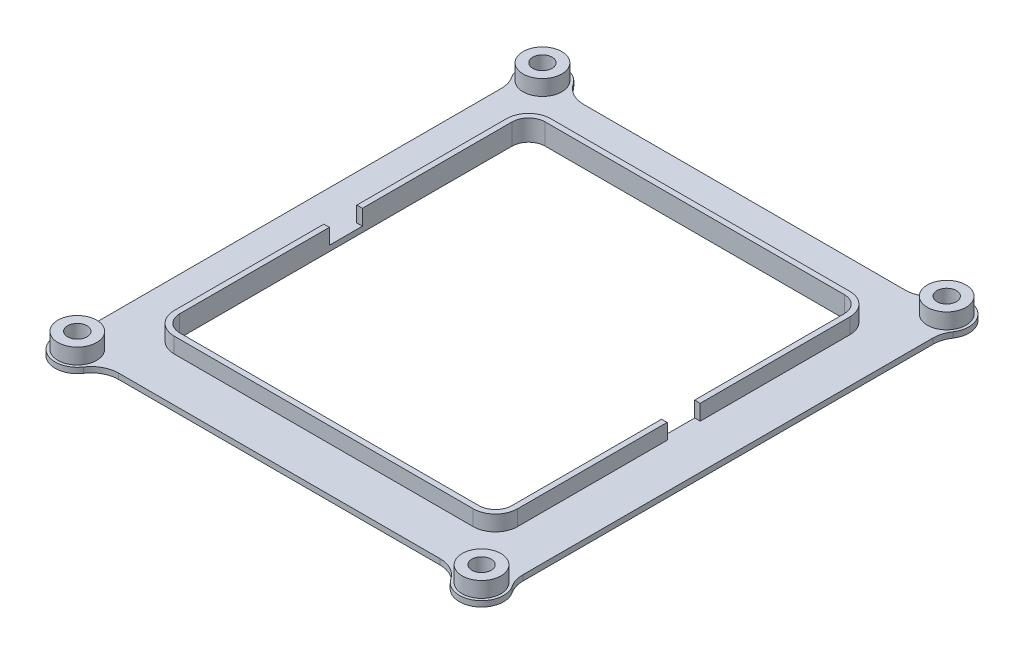
SolidWorks part; units mm, degrees
material "6061-T6 (SS)"
ref_plane "Front Plane" through (0, 0, 0) normal (0, 0, 1) x (1, 0, 0)
ref_plane "Top Plane" through (0, 0, 0) normal (0, 1, 0) x (1, 0, 0)
ref_plane "Right Plane" through (0, 0, 0) normal (1, 0, 0) x (0, 0, -1)
sketch "Sketch1" plane through (0, 0, 0) normal (0, 1, 0) x (1, 0, 0)
  line L0 (-33, 42) -> (33, 42)
  line L1 (-36.5, -42) -> (36.5, -42) construction
  line L2 (-36.5, -42) -> (-36.5, 42) construction
  line L3 (-36.5, 42) -> (36.5, 42) construction
  line L4 (36.5, -42) -> (36.5, 42) construction
  line L5 (-36.5, -42) -> (36.5, 42) construction
  line L6 (-36.5, 42) -> (36.5, -42) construction
  line L7 (36.5, 38.5) -> (36.5, -38.5)
  line L8 (33, -42) -> (-33, -42)
  line L9 (-36.5, -38.5) -> (-36.5, 38.5)
  line L11 (35.5, -41) -> (-35.5, -41)
  line L12 (35.5, -41) -> (35.5, 41)
  line L13 (35.5, 41) -> (-35.5, 41)
  line L14 (-35.5, -41) -> (-35.5, 41)
  line L15 (35.5, -41) -> (-35.5, 41) construction
  line L16 (35.5, 41) -> (-35.5, -41) construction
  circle A0 centre (-36.5, 42) radius 1.75
  circle A1 centre (36.5, 42) radius 1.75
  circle A2 centre (36.5, -42) radius 1.75
  circle A3 centre (-36.5, -42) radius 1.75
  circle A4 centre (-36.5, -42) radius 3.5
  circle A5 centre (-36.5, 42) radius 3.5
  circle A6 centre (36.5, 42) radius 3.5
  circle A7 centre (36.5, -42) radius 3.5
  point P0 (0, 0)
  point P22 (0, 0)
  dimension "D3" = 3.5
  dimension "D4" = 7
  dimension "D1" = 84
  dimension "D2" = 73
  dimension "D5" = 1
  dimension "D6" = 1
extrude "FrameAndBoltHoles" add sketch "Sketch1" along normal blind 3.8 contours A6 L0 A5 L13 | A5 L14 A0 L13 | L14 A5 L13 A0 | A5 L9 A4 L14 | A4 L11 A3 L14 | L11 A4 L14 A3 | A7 L11 A4 L8 | L12 A7 L11 A2 | A7 L12 A2 L11 | A7 L7 A6 L12 | L13 A6 L12 A1 | A6 L13 A1 L12
sketch "Sketch2" plane through (0, 0, 0) normal (0, 1, 0) x (1, 0, 0)
  line L0 (-35.5, -38.6459) -> (-35.5, 38.6459) construction
  line L1 (33.1459, 41) -> (-33.1459, 41) construction
  line L2 (-35.5, -38.6459) -> (-35.5, 38.6459)
  line L3 (33.1459, 41) -> (-33.1459, 41)
  circle A0 centre (-31, 36.5) radius 4.5
  arc A1 (-35.5, 38.6459) -> (-33.1459, 41) centre (-36.5, 42) ccw construction
  arc A2 (-35.5, 38.6459) -> (-33.1459, 41) centre (-36.5, 42) ccw
  dimension "D1" = 9
extrude "InsideFillet" add sketch "Sketch2" along normal up to surface (3.8 mm away) contours A2 L2 A0 L3
mirror "MirrorFillet" about plane through (0, 0, 0) normal (1, 0, 0) of "InsideFillet"
mirror "MirrorFillet2" about plane through (0, 0, 0) normal (0, 0, 1) of "MirrorFillet", "InsideFillet"
sketch "Sketch3" plane through (0, 0, 0) normal (0, 1, 0) x (1, 0, 0)
  line L0 (-27, 41) -> (-27, 30)
  line L1 (33.1459, 41) -> (-33.1459, 41) construction
  line L2 (-27, 30) -> (-35.5, 30)
  line L3 (-35.5, -36.5) -> (-35.5, 36.5) construction
  line L4 (-35.5, -36.5) -> (-35.5, 36.5)
  line L5 (33.1459, 41) -> (-31, 41)
  line L6 (-27, 33) -> (-19, 41)
  line L7 (33.1459, 41) -> (-33.1459, 41) construction
  line L8 (-30, 30) -> (-35.5, 24.5)
  line L9 (-27, 30) -> (27, 30) construction
  line L11 (-27, 30) -> (-27, -30) construction
  line L13 (27, 30) -> (35.5, 30) construction
  line L14 (35.5, -36.5) -> (35.5, 36.5) construction
  line L15 (-27, -30) -> (-27, -41) construction
  line L16 (33.1459, -41) -> (-33.1459, -41) construction
  circle A0 centre (-27, 30) radius 4
  circle A1 centre (-27, 30) radius 3
  arc A3 (-31, 41) -> (-35.5, 36.5) centre (-31, 36.5) ccw
  point P8 (-27, 34)
  point P9 (-31, 30)
  point P16 (27, 30)
  dimension "D1" = 54
  dimension "D3" = 8
  dimension "D4" = 6
  dimension "D2" = 60
  dimension "D5" = 45
  dimension "D6" = 45
extrude "WireTrough" add sketch "Sketch3" along normal blind 1 contours A0 L6 L5 L0 | L5 A3 L4 L2 A0 L0 | A0 L2 L4 L8 | L6 A0 L0 | A1 L0 A0 L2 | L2 A0 L8
sketch "Sketch4" plane through (0, 1, 0) normal (0, 1, 0) x (1, 0, 0)
  line L0 (-27, 33) -> (-19, 41) construction
  line L1 (-30, 30) -> (-35.5, 24.5) construction
  line L2 (-27, 33) -> (-19, 41)
  line L3 (-30, 30) -> (-35.5, 24.5)
  line L4 (0, 41) -> (0, 0) construction
  line L5 (0, 0) -> (-35.5, 0) construction
  line L6 (-35.5, -36.5) -> (-35.5, 24.5) construction
  line L7 (33.1459, 41) -> (-19, 41) construction
  line L8 (-27, 33) -> (0, 33)
  line L9 (0, 33) -> (0, 34)
  line L10 (0, 34) -> (-27, 34)
  line L11 (-30, 30) -> (-30, 0)
  line L12 (-31, 30) -> (-31, 0)
  line L13 (-31, 0) -> (-30, 0)
  line L14 (-27, 33) -> (-30, 30)
  circle A1 centre (-27, 30) radius 4
  arc A3 (-27, 33) -> (-30, 30) centre (-27, 30) ccw construction
  arc A4 (-27, 33) -> (-30, 30) centre (-27, 30) ccw
  arc A5 (-27, 33) -> (-30, 30) centre (-27, 30) ccw
  line M3 (-35.5, 24.5) -> (-30, 30)
  arc M4 (-30, 30) -> (-27, 33) centre (-27, 30) cw
  line M5 (-27, 33) -> (-19, 41)
  dimension "D1" = 8
extrude "WireInsideWall" add sketch "Sketch4" along normal up to surface (2.8 mm away) contours A1 L3 M5 M4 | A1 L8 L9 L10 L2 | L8 A1 M5 | A1 L11 M3 | A1 L3 L12 L13 L11 | A1 L2 L10 | A1 L12 L3 up to face at (0, 3.8, 0)
mirror "WireSpaceMirror" about plane through (0, 0, 0) normal (1, 0, 0) of "WireInsideWall", "WireTrough"
mirror "WireSpaceMirror2" about plane through (0, 0, 0) normal (0, 0, 1) of "WireSpaceMirror", "WireTrough", "WireInsideWall"
ref_plane "Plane1" through (0, 1.55, 0) normal (0, 1, 0) x (1, 0, 0)
sketch "Sketch6" plane through (0, 1.55, 0) normal (0, 1, 0) x (1, 0, 0)
  line L0 (-27, 30) -> (-27, 41) construction
  line L1 (-19, 41) -> (-31, 41) construction
  line L2 (-27, 30) -> (-35.5, 30) construction
  line L3 (-37.5, 30) -> (-37.5, 0)
  line L4 (-35.5, 24.5) -> (-35.5, 36.5) construction
  line L5 (0, 41) -> (0, 0) construction
  line L6 (33.1459, 41) -> (-33.1459, 41) construction
  line L7 (0, 0) -> (-35.5, 0) construction
  line L9 (-35.5, -36.5) -> (-35.5, 36.5) construction
  line L10 (-27, 40.5) -> (0, 40.5)
  line L11 (-27, 36) -> (-27, 37) construction
  line L12 (0, 39.5) -> (-27, 39.5)
  line L13 (-27, 39.5) -> (-27, 37) construction
  line L14 (-27, 37) -> (0, 37)
  line L15 (-27, 39.5) -> (-27, 40.5) construction
  line L16 (0, 36) -> (-27, 36)
  line L17 (-27, 40.5) -> (-27, 41) construction
  line L18 (-27, 35.5) -> (-27, 36) construction
  line L19 (-36.5, 0) -> (-36.5, 30)
  line L20 (-34, 30) -> (-34, 0)
  line L21 (-33, 30) -> (-33, 0)
  arc A0 (-27, 40.5) -> (-37.5, 30) centre (-27, 30) ccw
  arc A1 (-27, 39.5) -> (-36.5, 30) centre (-27, 30) ccw
  arc A2 (-27, 37) -> (-34, 30) centre (-27, 30) ccw
  arc A3 (-27, 36) -> (-33, 30) centre (-27, 30) ccw
  dimension "D1" = 0.5
  dimension "D2" = 1
  dimension "D3" = 1
  dimension "D4" = 0.5
sketch "Sketch7" plane through (0, 1, 0) normal (0, -1, 0) x (1, 0, 0)
  line L0 (19, -41) -> (-19, -41) construction
  line L1 (-35.5, 41) -> (35.5, 41)
  line L2 (-35.5, 41) -> (-35.5, -41)
  line L3 (-35.5, -41) -> (35.5, -41)
  line L4 (35.5, 41) -> (35.5, -41)
  line L5 (-35.5, 41) -> (35.5, -41) construction
  line L6 (-35.5, -41) -> (35.5, 41) construction
  line L7 (-30, 33) -> (30, 33)
  line L8 (-30, 33) -> (-30, -33)
  line L9 (-30, -33) -> (30, -33)
  line L10 (30, 33) -> (30, -33)
  line L11 (-30, 33) -> (30, -33) construction
  line L12 (-30, -33) -> (30, 33) construction
  line L13 (35.5, 24.5) -> (35.5, -24.5) construction
  line L14 (-27, -33) -> (27, -33) construction
  line L15 (30, -30) -> (30, 30) construction
  circle A0 centre (36.5, -42) radius 1.75
  circle A1 centre (-36.5, -42) radius 1.75
  circle A2 centre (-36.5, 42) radius 1.75
  circle A3 centre (36.5, 42) radius 1.75
  circle A5 centre (36.5, 42) radius 1.75 construction
  circle A6 centre (-36.5, 42) radius 1.75 construction
  circle A7 centre (-36.5, -42) radius 1.75 construction
  circle A8 centre (36.5, -42) radius 1.75 construction
  point P0 (0, 0)
  point P6 (0, 0)
  line M13 (27, -33) -> (-27, -33)
  line M14 (-27, -33) -> (-26, -34)
  line M15 (-26, -34) -> (26, -34)
  line M16 (26, -34) -> (27, -33)
extrude "InnerRing" add sketch "Sketch7" along normal up to surface (1 mm away) contours M16 M13 M14 M15 | A3 L1 A2 L2 A1 L3 A0 L4 L7 L10 L9 L8 M16 M15 M14 up to face at (0, 0, 0)
sketch "Sketch8" plane through (0, 3.8, 0) normal (0, 1, 0) x (1, 0, 0)
  line L0 (-27, 34) -> (27, 34) construction
  line L1 (31, -34) -> (-31, -34)
  line L2 (31, -34) -> (31, 34)
  line L3 (31, 34) -> (-31, 34)
  line L4 (-31, -34) -> (-31, 34)
  line L5 (31, -34) -> (-31, 34) construction
  line L6 (31, 34) -> (-31, -34) construction
  line L7 (50, -50) -> (-50, -50)
  line L8 (50, -50) -> (50, 50)
  line L9 (50, 50) -> (-50, 50)
  line L10 (-50, -50) -> (-50, 50)
  line L11 (50, -50) -> (-50, 50) construction
  line L12 (50, 50) -> (-50, -50) construction
  line L13 (-31, 30) -> (-31, -30) construction
  circle A0 centre (-36.5, 42) radius 3.5
  circle A1 centre (36.5, 42) radius 3.5
  circle A2 centre (36.5, -42) radius 3.5
  circle A3 centre (-36.5, -42) radius 3.5
  point P16 (0, 0)
  point P22 (0, 0)
  dimension "D1" = 100
  dimension "D2" = 100
extrude "RemoveOuterRing" cut sketch "Sketch8" against normal up to surface (2.8 mm away) up to face at (0, 1, 0)
sketch "Sketch9" plane through (0, 0, 0) normal (0, -1, 0) x (1, 0, 0)
  line L0 (0, 0) -> (0, -33) construction
  line L1 (-27, -33) -> (27, -33) construction
  line L2 (0, -33) -> (0, -46)
  line L5 (-40.5, 0) -> (-31, 0)
  line L6 (-31, 0) -> (0, 0) construction
  line L7 (-31, -30) -> (-31, 30) construction
  line L8 (-36.5, -46) -> (0, -46)
  line L9 (-40.5, -42) -> (-40.5, 0)
  circle A0 centre (-36.5, -42) radius 4
  circle A1 centre (-36.5, -42) radius 3.5 construction
  line M24 (-36.5, 38.5) -> (-36.5, -38.5)
  arc M25 (-36.5, -38.5) -> (-33, -42) centre (-36.5, -42) ccw
  line M26 (-33, -42) -> (33, -42)
  dimension "D1" = 0.5
extrude "Boss-Extrude2" add sketch "Sketch9" against normal up to surface (1 mm away) contours A0 M26 M25 M24
mirror "Mirror1" about plane through (0, 0, 0) normal (1, 0, 0) of "Boss-Extrude2"
mirror "Mirror2" about plane through (0, 0, 0) normal (0, 0, 1) of "Mirror1", "Boss-Extrude2"
sketch "Sketch10" plane through (0, 1, 0) normal (0, 1, 0) x (1, 0, 0)
  line L0 (36.5, 38) -> (36.5, -38) construction
  line L1 (36.5, -38.8775) -> (39, -38.8775)
  line L2 (36.5, -38.8775) -> (36.5, 39.5505)
  line L3 (36.5, 39.5505) -> (39, 39.5505)
  line L4 (39, -38.8775) -> (39, 39.5505)
  line L5 (-36.5, -39.5505) -> (-39, -39.5505)
  line L6 (-36.5, -39.5505) -> (-36.5, 39.5505)
  line L7 (-36.5, 39.5505) -> (-39, 39.5505)
  line L8 (-39, -39.5505) -> (-39, 39.5505)
  line L11 (-36.5, -38) -> (-36.5, 38) construction
  circle A1 centre (36.5, 42) radius 3.5 construction
  circle A3 centre (-36.5, 42) radius 3.5 construction
  arc A4 (32.5, -42) -> (36.5, -38) centre (36.5, -42) ccw construction
  circle A5 centre (-36.5, -42) radius 3.5 construction
  dimension "D1" = 2.5
  dimension "D2" = 2.5
extrude "Boss-Extrude3" add sketch "Sketch10" against normal up to surface (1 mm away) up to face at (0, 0, 0)
fillet "Fillet1" radius 5 8 edges at (-32.5, 0.5, -42) (32.5, 0.5, -42) (39, 0.5, -38.8775) (39, 0.5, 38.8775) (32.5, 0.5, 42) (-32.5, 0.5, 42) (-39, 0.5, 38.8775) (-39, 0.5, -38.8775)
sketch "Sketch11" plane through (0, 3.8, 0) normal (0, 1, 0) x (1, 0, 0)
  line L2 (0, 0) -> (0, -65.5856) construction
  line L3 (31, 0) -> (30, 0) construction
  line L4 (31, 30) -> (31, -30) construction
  line L5 (30, 30) -> (30, -30) construction
  circle A0 centre (30.5, 0) radius 3
  circle A1 centre (-30.5, 0) radius 3
  dimension "D1" = 6
extrude "Cut-Extrude1" cut sketch "Sketch11" against normal up to surface (2.8 mm away) up to face at (-36.5, 1, -38.5)
